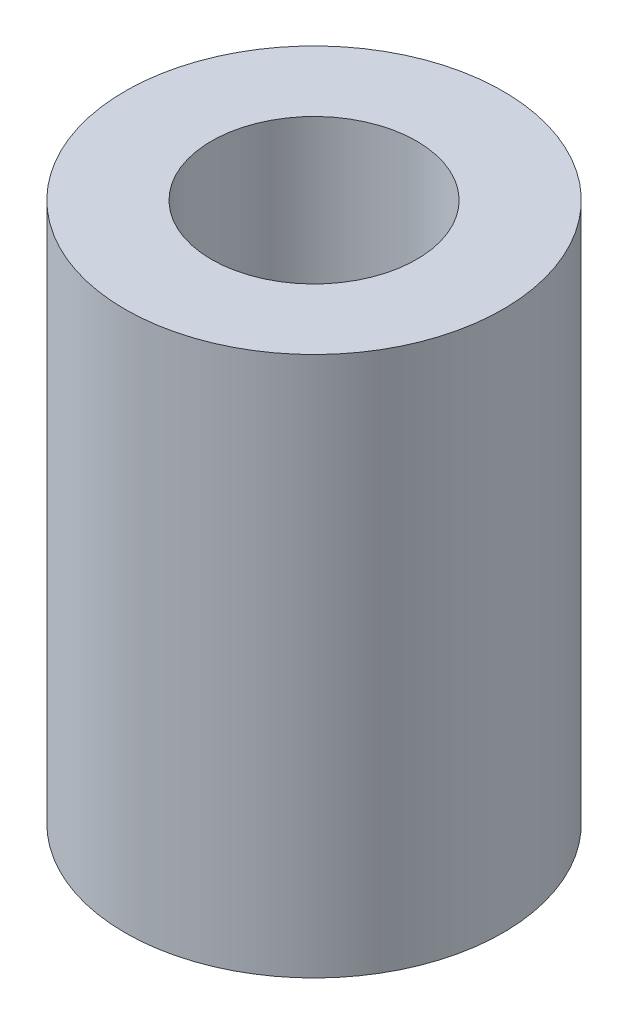
SolidWorks part; units mm, degrees
ref_plane "Front Plane" through (0, 0, 0) normal (0, 0, 1) x (1, 0, 0)
ref_plane "Top Plane" through (0, 0, 0) normal (0, 1, 0) x (1, 0, 0)
ref_plane "Right Plane" through (0, 0, 0) normal (1, 0, 0) x (0, 0, -1)
sketch "Sketch1" plane through (0, 0, 0) normal (0, 1, 0) x (1, 0, 0)
  circle A0 centre (0, 0) radius 1.75
  circle A1 centre (0, 0) radius 0.95
  dimension "D1" = 1.9
  dimension "D2" = 3.5
extrude "Boss-Extrude1" add sketch "Sketch1" along normal blind 5
